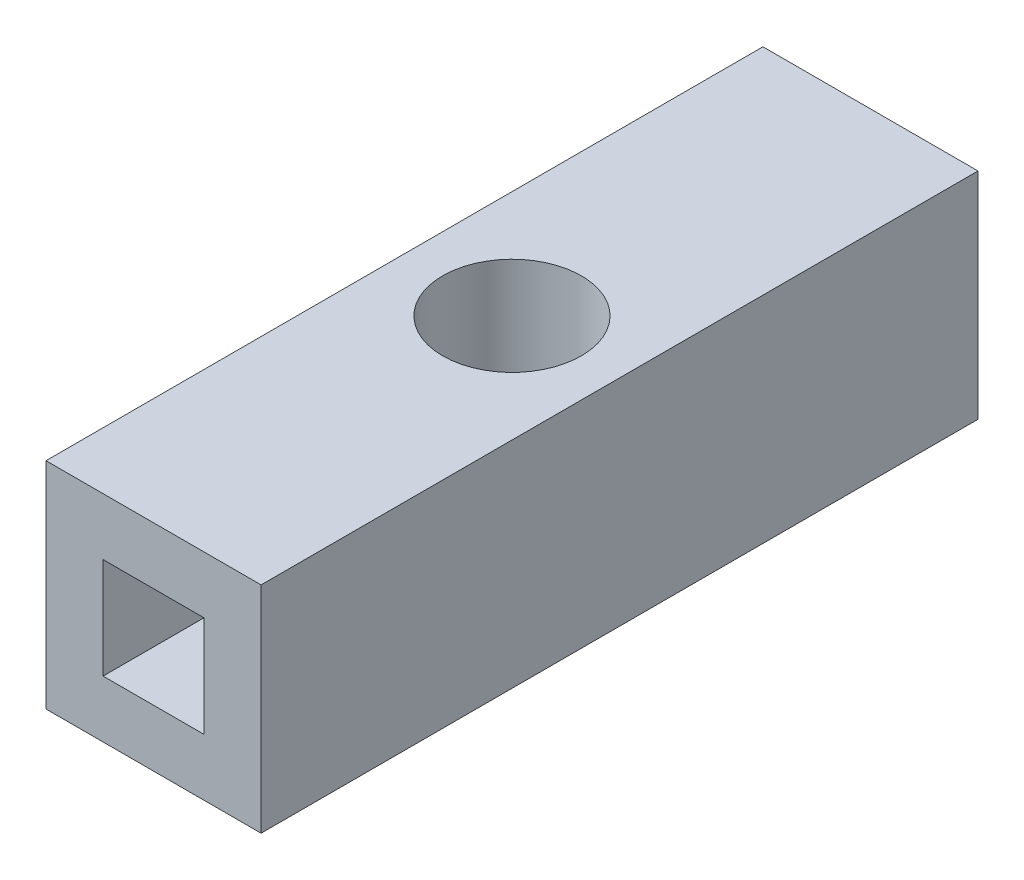
SolidWorks part; units mm, degrees
ref_plane "Front Plane" through (0, 0, 0) normal (0, 0, 1) x (1, 0, 0)
ref_plane "Top Plane" through (0, 0, 0) normal (0, 1, 0) x (1, 0, 0)
ref_plane "Right Plane" through (0, 0, 0) normal (1, 0, 0) x (0, 0, -1)
sketch "Sketch2" plane through (0, 0, 0) normal (0, 0, 1) x (1, 0, 0)
  line L1 (-3.81, 3.81) -> (3.81, 3.81)
  line L2 (-3.81, 3.81) -> (-3.81, -3.81)
  line L3 (-3.81, -3.81) -> (3.81, -3.81)
  line L4 (3.81, 3.81) -> (3.81, -3.81)
  line L5 (-3.81, 3.81) -> (3.81, -3.81) construction
  line L6 (-3.81, -3.81) -> (3.81, 3.81) construction
  point P0 (0, 0)
  dimension "D1" = 7.62
extrude "Boss-Extrude1" add sketch "Sketch2" along normal mid plane 25.4
hole_wizard "#8 Clearance Hole1" positions "Sketch3" profile "Sketch4" hole size "#8" standard "ANSI Inch" end condition up to next
sketch "Sketch3" plane through (0, 3.81, 0) normal (0, 1, 0) x (1, 0, 0)
  point P0 (0, 0)
sketch "Sketch4" plane through (0, 3.81, 0) normal (1, 0, 0) x (0, 0, 1)
  line L0 (0, 0) -> (0, 7.62)
  line L1 (0, 7.62) -> (2.4574, 7.62)
  line L2 (2.4574, 7.62) -> (2.4574, 0)
  line L5 (2.4574, 0) -> (0, 0)
  line L11 (0, -6.35) -> (0, 107.95) construction
  dimension "Thru Hole Dia." = 4.9149
  dimension "Thru Hole Depth" = 7.62
sketch "Sketch5" plane through (0, 0, 12.7) normal (0, 0, 1) x (1, 0, 0)
  line L1 (-1.5875, 1.5875) -> (1.5875, 1.5875)
  line L2 (-1.5875, 1.5875) -> (-1.5875, -1.5875)
  line L3 (-1.5875, -1.5875) -> (1.5875, -1.5875)
  line L4 (1.5875, 1.5875) -> (1.5875, -1.5875)
  line L5 (-1.5875, 1.5875) -> (1.5875, -1.5875) construction
  line L6 (-1.5875, -1.5875) -> (1.5875, 1.5875) construction
  point P0 (0, 0)
  dimension "D1" = 3.175
extrude "Cut-Extrude1" cut sketch "Sketch5" against normal offset from surface (9.6106 mm away) 1.016
sketch "Sketch6" plane through (0, 0, -12.7) normal (0, 0, -1) x (-1, 0, 0)
  line L0 (1.5, 1.3229) -> (1.5, -1.3229)
  arc A0 (1.5, 1.3229) -> (1.5, -1.3229) centre (0, 0) ccw
  point P1 (0, 0)
  point P5 (-2, 0)
  point P6 (1.7694, -0.9576)
  point P7 (0, 0)
  point P8 (0, 0)
  dimension "D1" = 4
  dimension "D2" = 3.5
extrude "Cut-Extrude2" cut sketch "Sketch6" against normal offset from surface (9.5671 mm away) 1.016 contours A0 L0
sketch "Sketch7" plane through (0, 0, 12.7) normal (0, 0, 1) x (1, 0, 0)
  line L0 (-1.5875, -1.5875) -> (1.5875, -1.5875) construction
  line L1 (1.5875, -1.5875) -> (1.5875, 1.5875) construction
  line L2 (-1.5875, 1.5875) -> (-1.5875, -1.5875) construction
  line L3 (1.5875, 1.5875) -> (-1.5875, 1.5875) construction
  line L4 (-1.5875, -1.5875) -> (1.5875, -1.5875)
  line L5 (1.5875, -1.5875) -> (1.5875, 1.5875)
  line L6 (-1.5875, 1.5875) -> (-1.5875, -1.5875)
  line L7 (1.5875, 1.5875) -> (-1.5875, 1.5875)
  line L8 (-1.7875, 1.7875) -> (-1.7875, -1.7875)
  line L9 (-1.7875, -1.7875) -> (1.7875, -1.7875)
  line L10 (1.7875, -1.7875) -> (1.7875, 1.7875)
  line L11 (1.7875, 1.7875) -> (-1.7875, 1.7875)
  dimension "D1" = 0.2
extrude "Cut-Extrude3" cut sketch "Sketch7" against normal up to surface (9.6106 mm away)
sketch "Sketch8" plane through (0, 0, -12.7) normal (0, 0, -1) x (-1, 0, 0)
  line L2 (1.7, -1.3964) -> (1.7, 1.3964)
  line L3 (1.7, -1.3964) -> (1.7, 1.3964)
  arc A2 (1.7, 1.3964) -> (1.7, -1.3964) centre (0, 0) ccw
  arc A3 (1.7, 1.3964) -> (1.7, -1.3964) centre (0, 0) ccw
  dimension "D1" = 0.2
extrude "Cut-Extrude4" cut sketch "Sketch8" against normal up to surface (9.671 mm away)
equation "\"D1@Sketch6\"=4mm"
